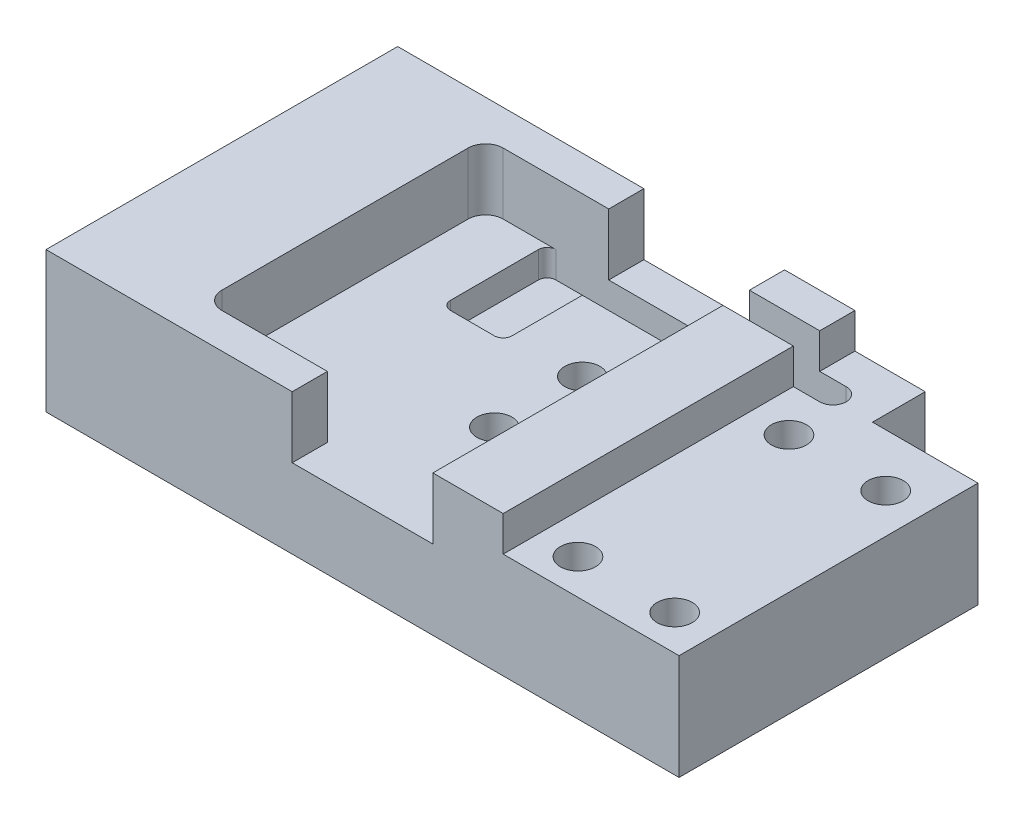
SolidWorks part; units mm, degrees
other "标注1"
sketch "草图12" plane through (-36, 0, -20) normal (0, 0, -1) x (-1, 0, 0)
other "标注2"
sketch "草图13" plane through (0, 0, -20) normal (0.0271, -0.9975, -0.0646) x (0.9672, 0.0099, 0.254)
ref_plane "前视基准面" through (0, 0, 0) normal (0, 0, 1) x (1, 0, 0)
ref_plane "上视基准面" through (0, 0, 0) normal (0, 1, 0) x (1, 0, 0)
ref_plane "右视基准面" through (0, 0, 0) normal (1, 0, 0) x (0, 0, -1)
sketch "草图1" plane through (0, 0, 0) normal (0, 1, 0) x (1, 0, 0)
  line L1 (0, 0) -> (-36, 0)
  line L2 (0, 0) -> (0, 20)
  line L3 (0, 20) -> (-36, 20)
  line L4 (-36, 0) -> (-36, 20)
  dimension "D1" = 36
  dimension "D2" = 20
extrude "凸台-拉伸1" add sketch "草图1" along normal blind 8
sketch "草图2" plane through (0, 8, 0) normal (0, 1, 0) x (1, 0, 0)
  line L0 (0, 20) -> (-36, 20) construction
  line L1 (-14, 20) -> (-22, 20)
  line L2 (-14, 20) -> (-14, 0)
  line L3 (-14, 0) -> (-22, 0)
  line L4 (-22, 20) -> (-22, 0)
  line L5 (-36, 0) -> (0, 0) construction
  line L6 (0, 10) -> (-14, 10) construction
  line L7 (0, 0) -> (0, 20) construction
  line L8 (-22, 10) -> (-36, 10) construction
  line L9 (-36, 20) -> (-36, 0) construction
  dimension "D1" = 8
extrude "切除-拉伸1" cut sketch "草图2" against normal blind 3.5
sketch "草图3" plane through (0, 0, 0) normal (0, -1, 0) x (-1, 0, 0)
  line L0 (0, 10) -> (8, 10) construction
  line L3 (0, 0) -> (0, 20) construction
  line L4 (28, 10) -> (36, 10) construction
  line L5 (36, 20) -> (36, 0) construction
  circle A2 centre (8, 10) radius 2.5
  circle A3 centre (28, 10) radius 2.5
  dimension "D1" = 5
  dimension "D2" = 20
extrude "切除-拉伸2" cut sketch "草图3" against normal blind 4
sketch "草图5" plane through (0, 8, 0) normal (0, 1, 0) x (1, 0, 0)
  line L0 (-22, 20) -> (-22, 0) construction
  line L1 (-22, 18) -> (-29, 18)
  line L2 (-22, 18) -> (-22, 2)
  line L3 (-22, 2) -> (-29, 2)
  line L4 (-29, 18) -> (-29, 2)
  line L5 (-25.5, 18) -> (-25.5, 20) construction
  line L6 (-22, 20) -> (-36, 20) construction
  line L7 (-25.5, 2) -> (-25.5, 0) construction
  line L8 (-36, 0) -> (-22, 0) construction
  dimension "D1" = 16
  dimension "D2" = 7
extrude "切除-拉伸4" cut sketch "草图5" against normal blind 3.5
fillet "圆角1" radius 1 2 edges at (-29, 6.25, -2) (-29, 6.25, -18)
sketch "草图6" plane through (0, 4.5, 0) normal (0, 1, 0) x (1, 0, 0)
  line L0 (-18, 20) -> (-18, 12.5) construction
  line L1 (-18, 7.5) -> (-18, 0) construction
  line L2 (-22, 0) -> (-14, 0) construction
  line L3 (-14, 20) -> (-22, 20) construction
  circle A0 centre (-18, 12.5) radius 1
  circle A1 centre (-18, 7.5) radius 1
  dimension "D2" = 2
  dimension "D1" = 5
extrude "切除-拉伸5" cut sketch "草图6" against normal through all
sketch "草图7" plane through (0, 8, 0) normal (0, 1, 0) x (1, 0, 0)
  line L0 (-14, 0) -> (0, 0) construction
  line L1 (0, 20) -> (-10, 20)
  line L2 (0, 20) -> (0, 0)
  line L3 (0, 0) -> (-10, 0)
  line L4 (-10, 20) -> (-10, 0)
  dimension "D1" = 10
extrude "切除-拉伸6" cut sketch "草图7" against normal blind 2
sketch "草图9" plane through (0, 6, 0) normal (0, 1, 0) x (1, 0, 0)
  line L0 (-2.25, 2) -> (-7.75, 2) construction
  line L1 (-7.75, 2) -> (-7.75, 14) construction
  line L2 (-7.75, 14) -> (-2.25, 14) construction
  line L3 (-2.25, 14) -> (-2.25, 2) construction
  line L6 (-2.25, 2) -> (-2.25, 0) construction
  line L7 (-10, 0) -> (0, 0) construction
  line L8 (-2.25, 2) -> (0, 2) construction
  line L9 (0, 0) -> (0, 20) construction
  line L10 (-7.75, 2) -> (-10, 2) construction
  line L11 (-10, 20) -> (-10, 0) construction
  circle A0 centre (-2.25, 2) radius 1
  circle A1 centre (-7.75, 2) radius 1
  circle A2 centre (-2.25, 14) radius 1
  circle A3 centre (-7.75, 14) radius 1
  dimension "D1" = 2
  dimension "D2" = 5.5
  dimension "D3" = 12
  dimension "D4" = 2
extrude "切除-拉伸10" cut sketch "草图9" against normal blind 3
sketch "草图10" plane through (0, 0, 0) normal (0, -1, 0) x (-1, 0, 0)
  circle A0 centre (18, 12.5) radius 2
  circle A1 centre (18, 7.5) radius 2
  dimension "D1" = 4
  dimension "D2" = 4
extrude "切除-拉伸11" cut sketch "草图10" against normal blind 2.4
sketch "草图11" plane through (0, 0, -20) normal (0, 0, -1) x (-1, 0, 0)
  line L0 (0, 3) -> (3, 3) construction
  line L1 (0, 6) -> (0, 0) construction
  line L2 (33, 3) -> (36, 3) construction
  line L3 (36, 8) -> (36, 0) construction
  line L4 (0, 0) -> (36, 0) construction
  line L10 (0, 0) -> (6, 0)
  line L11 (0, 0) -> (0, 6)
  line L12 (0, 6) -> (6, 6)
  line L13 (6, 0) -> (6, 6)
  line L14 (36, 0) -> (30, 0)
  line L15 (36, 0) -> (36, 6)
  line L16 (36, 6) -> (30, 6)
  line L17 (30, 0) -> (30, 6)
  circle A0 centre (3, 3) radius 2.85 construction
  circle A1 centre (33, 3) radius 2.85 construction
  dimension "D2" = 5.7
  dimension "D1" = 3
  dimension "D3" = 30
  dimension "D4" = 6
extrude "切除-拉伸15" cut sketch "草图11" against normal blind 3
sketch "草图14" plane through (0, 4.5, 0) normal (0, 1, 0) x (1, 0, 0)
  line L1 (-22, 18) -> (-25.5, 18)
  line L2 (-22, 18) -> (-22, 12)
  line L3 (-22, 12) -> (-25.5, 12)
  line L4 (-25.5, 18) -> (-25.5, 12)
  dimension "D1" = 6
  dimension "D2" = 3.5
extrude "切除-拉伸17" cut sketch "草图14" against normal blind 1.5
fillet "圆角4" radius 0.5 4 edges at (-25.5, 3.75, -12) (-22, 3.75, -12) (-25.5, 3.75, -18) (-22, 3.75, -18)
sketch "草图15" plane through (0, 3, 0) normal (0, 1, 0) x (1, 0, 0)
  line L0 (-25.5, 17.5) -> (-25.5, 12.5) construction
  line L1 (-25.5, 16.5) -> (-8.5, 16.5)
  line L2 (-25.5, 16.5) -> (-25.5, 18)
  line L3 (-25.5, 18) -> (-8.5, 18)
  line L6 (-22, 18) -> (-28, 18) construction
  line L8 (-10, 20) -> (-10, 0) construction
  arc A1 (-8.5, 16.5) -> (-8.5, 18) centre (-8.5, 17.25) ccw
  dimension "D1" = 1.5
  dimension "D2" = 1.5
extrude "切除-拉伸18" cut sketch "草图15" along normal blind 28
fillet "圆角5" radius 0.5 1 edges at (-25.5, 3.75, -18)
fillet "圆角6" radius 2 1 edges at (-30, 6, -18.5)
